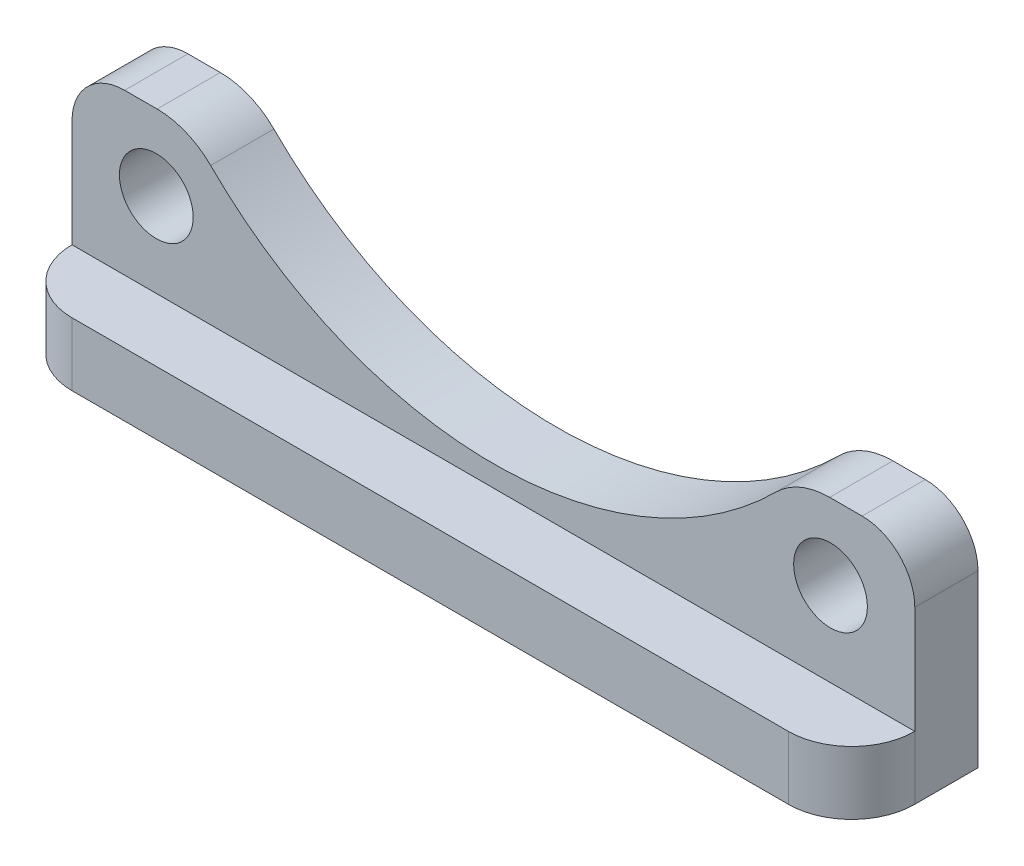
SolidWorks part; units mm, degrees
ref_plane "Plano frontal" through (0, 0, 0) normal (0, 0, 1) x (1, 0, 0)
ref_plane "Plano superior" through (0, 0, 0) normal (0, 1, 0) x (1, 0, 0)
ref_plane "Plano direito" through (0, 0, 0) normal (1, 0, 0) x (0, 0, -1)
sketch "Esboço1" plane through (0, 0, 0) normal (0, 0, 1) x (1, 0, 0)
  line L1 (-20, 5.3) -> (20, 5.3)
  line L2 (-20, 5.3) -> (-20, -5.3)
  line L3 (-20, -5.3) -> (20, -5.3)
  line L4 (20, 5.3) -> (20, -5.3)
  line L5 (-20, 5.3) -> (20, -5.3) construction
  line L6 (-20, -5.3) -> (20, 5.3) construction
  point P0 (0, 0)
  dimension "D1" = 40
  dimension "D2" = 10.6
extrude "Ressalto-extrusão1" add sketch "Esboço1" along normal blind 3
sketch "Esboço2" plane through (0, 0, 3) normal (0, 0, 1) x (1, 0, 0)
  line L0 (20, -5.3) -> (20, 5.3) construction
  line L1 (-20, -5.3) -> (20, -5.3)
  line L2 (-20, -5.3) -> (-20, -2.3)
  line L3 (-20, -2.3) -> (20, -2.3)
  line L4 (20, -5.3) -> (20, -2.3)
  dimension "D1" = 3
extrude "Ressalto-extrusão2" add sketch "Esboço2" along normal blind 3
fillet "Filete1" radius 3 2 edges at (-20, -3.8, 6) (20, -3.8, 6)
sketch "Esboço3" plane through (0, 0, 0) normal (0, 0, -1) x (-1, 0, 0)
  line L0 (20, -5.3) -> (-20, -5.3) construction
  line L1 (20, -5.3) -> (-20, -5.3)
  line L2 (20, 1.7) -> (-20, 1.7) construction
  line L3 (-16, 1.7) -> (16, 1.7) construction
  line L4 (0, -5.3) -> (0, 17.7) construction
  circle A0 centre (-16, 1.7) radius 1.75
  circle A1 centre (16, 1.7) radius 1.75
  circle A2 centre (0, 17.7) radius 19
  point P7 (0, 1.7)
  line M7 (20, 5.3) -> (-20, 5.3)
  dimension "D3" = 3.5
  dimension "D5" = 38
  dimension "D2" = 32
  dimension "D4" = 23
  dimension "D1" = 7
extrude "Corte-extrusão1" cut sketch "Esboço3" against normal up to surface (3 mm away) contours A2 M7 | A1 | A0 up to face at (0, 1.5, 3)
fillet "Filete2" radius 2.5 2 edges at (-20, 5.3, 1.5) (20, 5.3, 1.5)
fillet "Filete3" radius 3.6 2 edges at (14.3958, 5.3, 1.5) (-14.3958, 5.3, 1.5)
